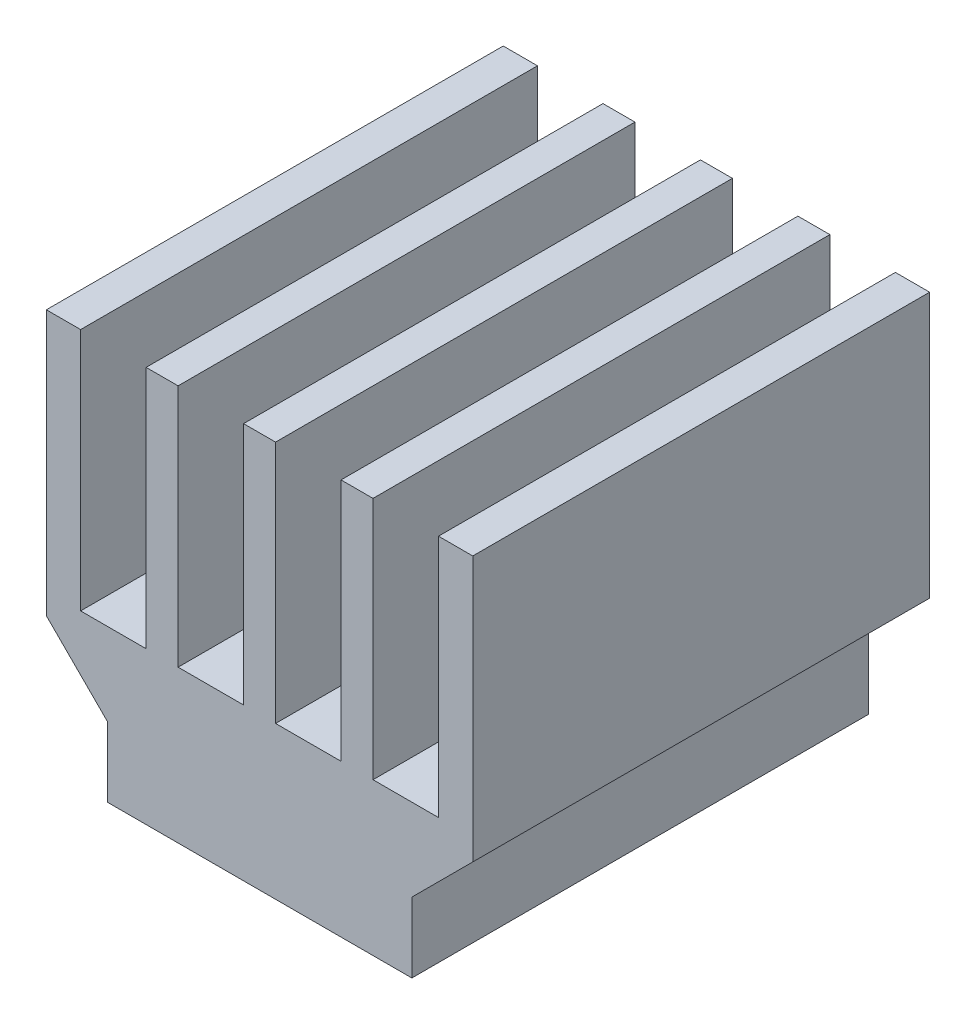
SolidWorks part; units mm, degrees
material "6061-T6 (SS)"
ref_plane "Front Plane" through (0, 0, 0) normal (0, 0, 1) x (1, 0, 0)
ref_plane "Top Plane" through (0, 0, 0) normal (0, 1, 0) x (1, 0, 0)
ref_plane "Right Plane" through (0, 0, 0) normal (1, 0, 0) x (0, 0, -1)
sketch "Sketch1" plane through (0, 0, 0) normal (0, 0, 1) x (1, 0, 0)
  line L0 (-7, 13) -> (-7, 0)
  line L1 (-7, 13) -> (7, 13)
  line L2 (-7, 0) -> (7, 0)
  line L3 (7, 13) -> (7, 0)
  line L4 (-7, 13) -> (7, 0) construction
  line L5 (-7, 0) -> (7, 13) construction
  line L6 (7, 4.3) -> (5, 2.3)
  line L7 (5, 2.3) -> (5, 0)
  line L8 (0, 13) -> (0, 0) construction
  line L9 (-0.525, 13) -> (-0.525, 5)
  line L10 (0.525, 13) -> (2.675, 13)
  line L11 (0.525, 13) -> (0.525, 5)
  line L12 (0.525, 5) -> (2.675, 5)
  line L13 (2.675, 13) -> (2.675, 5)
  line L14 (3.725, 13) -> (5.875, 13)
  line L15 (3.725, 13) -> (3.725, 5)
  line L16 (3.725, 5) -> (5.875, 5)
  line L17 (5.875, 13) -> (5.875, 5)
  line L18 (-0.525, 5) -> (-2.675, 5)
  line L19 (-2.675, 13) -> (-2.675, 5)
  line L20 (-3.725, 13) -> (-3.725, 5)
  line L21 (-3.725, 5) -> (-5.875, 5)
  line L22 (-5.875, 13) -> (-5.875, 5)
  line L23 (-5, 2.3) -> (-5, 0)
  line L24 (-7, 4.3) -> (-5, 2.3)
  point P1 (0, 6.5)
  point P3 (0, 0)
  dimension "D1" = 14
  dimension "D2" = 13
  dimension "D3" = 4.3
  dimension "D4" = 2
  dimension "D5" = 135
  dimension "D6" = 2.15
  dimension "D7" = 0.525
  dimension "D8" = 8
  dimension "D9" = 1.05
  dimension "D10" = 2.15
extrude "Boss-Extrude1" add sketch "Sketch1" along normal blind 15 contours L0 L24 L23 L2 L7 L6 L3 L1 L17 L16 L15 L13 L12 L11 L9 L18 L19 L20 L21 L22
equation "\"D10@Sketch1\"=\"D6@Sketch1\""
